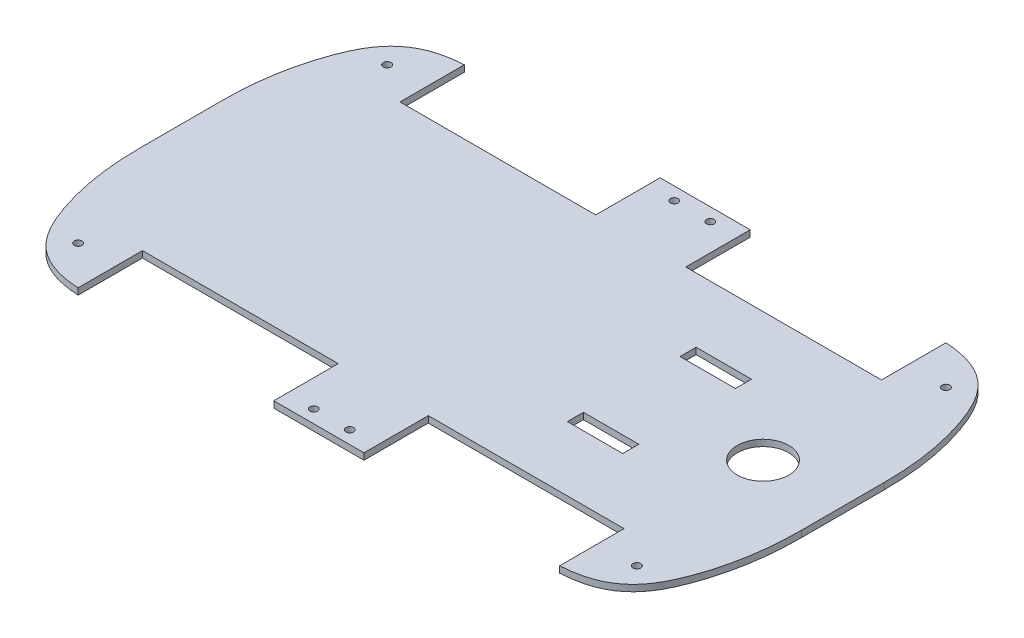
SolidWorks part; units mm, degrees
ref_plane "前视基准面" through (0, 0, 0) normal (0, 0, 1) x (1, 0, 0)
ref_plane "上视基准面" through (0, 0, 0) normal (0, 1, 0) x (1, 0, 0)
ref_plane "右视基准面" through (0, 0, 0) normal (1, 0, 0) x (0, 0, -1)
sketch "草图1" plane through (0, 0, 0) normal (0, 1, 0) x (1, 0, 0)
  line L0 (-93.5, 75) -> (-93.5, -3.1122) construction
  line L2 (-128.5, -16) -> (-128.5, 16)
  line L7 (170.1645, 0) -> (-170.1645, 0) construction
  line L8 (0, 0) -> (0, 83.7996) construction
  line L9 (-17.5, 50) -> (17.5, 50) construction
  line L10 (-108.5, 106.3258) -> (-108.5, -99.0524) construction
  line L11 (128.5, -16) -> (128.5, 16)
  line L12 (-93.5, 75) -> (-93.5, 50)
  line L13 (-93.5, 50) -> (-17.5, 50)
  line L14 (-17.5, 50) -> (-17.5, 75)
  line L15 (-17.5, 75) -> (17.5, 75)
  line L16 (17.5, 50) -> (17.5, 75)
  line L17 (93.5, 50) -> (17.5, 50)
  line L18 (93.5, 75) -> (93.5, 50)
  line L20 (93.5, -75) -> (93.5, -50)
  line L21 (93.5, -50) -> (17.5, -50)
  line L22 (17.5, -50) -> (17.5, -75)
  line L23 (-17.5, -75) -> (17.5, -75)
  line L24 (-17.5, -50) -> (-17.5, -75)
  line L25 (-93.5, -50) -> (-17.5, -50)
  line L26 (-93.5, -75) -> (-93.5, -50)
  circle A0 centre (-108.5, 60) radius 1.5
  circle A1 centre (-108.5, -60) radius 1.5
  circle A2 centre (108.5, -60) radius 1.5
  circle A3 centre (108.5, 60) radius 1.5
  circle A5 centre (7, 70) radius 1.5
  circle A6 centre (-7, 70) radius 1.5
  circle A7 centre (7, -70) radius 1.5
  circle A8 centre (-7, -70) radius 1.5
  spline S0 degree 3 poles (-93.5, 75) (-111.6176, 74.0099) (-123.1338, 57.2411) (-128.5, 30.4474) (-128.5, 16) knots 0 0 0 0 0.426209 0.752893 0.752893 0.752893 0.752893
  spline S1 degree 3 poles (-93.5, -75) (-111.6176, -74.0099) (-123.1338, -57.2411) (-128.5, -30.4474) (-128.5, -16) knots 0 0 0 0 0.426209 0.752893 0.752893 0.752893 0.752893
  spline S2 degree 3 poles (93.5, -75) (111.6176, -74.0099) (123.1338, -57.2411) (128.5, -30.4474) (128.5, -16) knots 0 0 0 0 0.426209 0.752893 0.752893 0.752893 0.752893
  spline S3 degree 3 poles (93.5, 75) (111.6176, 74.0099) (123.1338, 57.2411) (128.5, 30.4474) (128.5, 16) knots 0 0 0 0 0.426209 0.752893 0.752893 0.752893 0.752893
  point P55 (-128.5, 0)
  dimension "D10" = 3
  dimension "D11" = 14
  dimension "D12" = 3
  dimension "D14" = 32
  dimension "D4" = 257
  dimension "D16" = 0
  dimension "D2" = 150
  dimension "D3" = 35
  dimension "D5" = 35
  dimension "D6" = 35
  dimension "D7" = 100
  dimension "D8" = 15
  dimension "D9" = 10
  dimension "D13" = 5
  dimension "D15" = 5.8147
extrude "凸台-拉伸1" add sketch "草图1" along normal blind 2.5
sketch "草图2" plane through (0, 2.5, 0) normal (0, 1, 0) x (1, 0, 0)
  line L0 (0, 0) -> (187.5935, 0) construction
  line L1 (93.5, 50) -> (17.5, 50) construction
  line L2 (46.5, 25) -> (68, 25)
  line L3 (46.5, 25) -> (46.5, 18.75)
  line L4 (46.5, 18.75) -> (68, 18.75)
  line L5 (68, 25) -> (68, 18.75)
  line L6 (17.5, 50) -> (17.5, 75) construction
  line L7 (46.5, -18.75) -> (68, -18.75)
  line L8 (68, -25) -> (68, -18.75)
  line L9 (46.5, -25) -> (68, -25)
  line L10 (46.5, -25) -> (46.5, -18.75)
  dimension "D1" = 25
  dimension "D2" = 6.25
  dimension "D3" = 29
  dimension "D4" = 21.5
extrude "切除-拉伸1" cut sketch "草图2" against normal through all
sketch "草图3" plane through (0, 2.5, 0) normal (0, 1, 0) x (1, 0, 0)
  line L0 (0, 0) -> (182.1407, 0) construction
  line L1 (128.5, -16) -> (128.5, 16) construction
  circle A0 centre (97.5, 0) radius 10
  dimension "D1" = 20
  dimension "D2" = 31
extrude "切除-拉伸2" cut sketch "草图3" against normal through all
